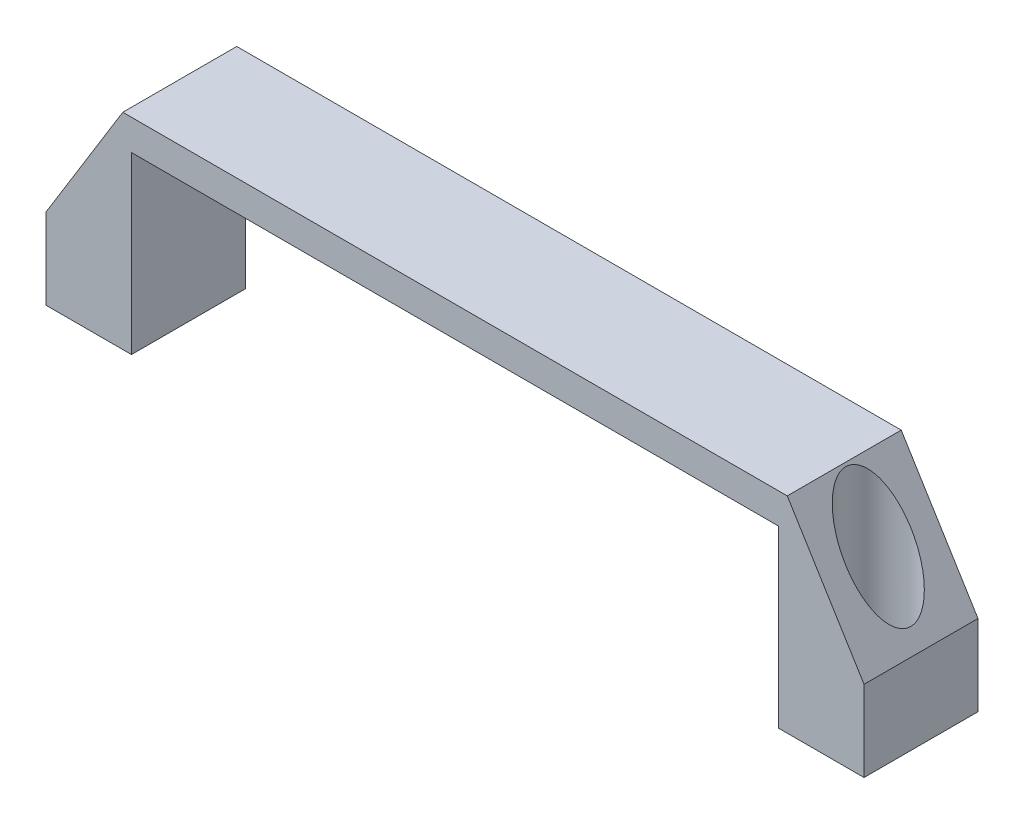
SolidWorks part; units mm, degrees
material "6061 合金"
ref_plane "前视基准面" through (0, 0, 0) normal (0, 0, 1) x (1, 0, 0)
ref_plane "上视基准面" through (0, 0, 0) normal (0, 1, 0) x (1, 0, 0)
ref_plane "右视基准面" through (0, 0, 0) normal (1, 0, 0) x (0, 0, -1)
sketch "草图1" plane through (0, 0, 0) normal (0, 0, 1) x (1, 0, 0)
  line L0 (0, 37.552) -> (0, -27.7826) construction
  line L1 (0, -55) -> (0, 55) construction
  line L2 (-17.9415, 0) -> (15.2637, 0) construction
  line L3 (55, 0) -> (-55, 0) construction
  line L4 (-100.5, -42.9917) -> (-79.5, -42.9917)
  line L5 (-79.5, -42.9917) -> (-79.5, 0.0083)
  line L6 (-79.5, 0.0083) -> (79.5, 0.0083)
  line L7 (-100.5, -42.9917) -> (-100.5, -23.1512)
  line L8 (-100.5, -23.1512) -> (-81.6322, 7.5083)
  line L9 (-81.6322, 7.5083) -> (81.6322, 7.5083)
  line L10 (100.5, -23.1512) -> (81.6322, 7.5083)
  line L11 (100.5, -42.9917) -> (100.5, -23.1512)
  line L12 (79.5, -42.9917) -> (79.5, 0.0083)
  line L13 (100.5, -42.9917) -> (79.5, -42.9917)
  point P17 (0, 7.5083)
  point P20 (0, 0.0083)
  dimension "D1" = 21
  dimension "D2" = 159
  dimension "D3" = 43
  dimension "D4" = 36
  dimension "D5" = 7.5
extrude "凸台-拉伸1" add sketch "草图1" along normal mid plane 28
sketch "草图3" plane through (0, -42.9917, 0) normal (0, -1, 0) x (1, 0, 0)
  line L0 (55, 0) -> (-55, 0) construction
  line L1 (0, 0) -> (0, -42.8363) construction
  line L2 (0, -55) -> (0, 55) construction
  circle A0 centre (-90, 0) radius 4.25
  circle A1 centre (90, 0) radius 4.25
  dimension "D1" = 8.5
  dimension "D2" = 180
extrude "切除-拉伸1" cut sketch "草图3" against normal through all
sketch "草图4" plane through (0, 7.5083, 0) normal (0, 1, 0) x (1, 0, 0)
  line L0 (0, 19.6299) -> (0, -35.5892) construction
  line L1 (0, -55) -> (0, 55) construction
  circle A0 centre (-90, 0) radius 8
  circle A1 centre (90, 0) radius 8
  dimension "D1" = 16
extrude "切除-拉伸2" cut sketch "草图4" against normal blind 46
